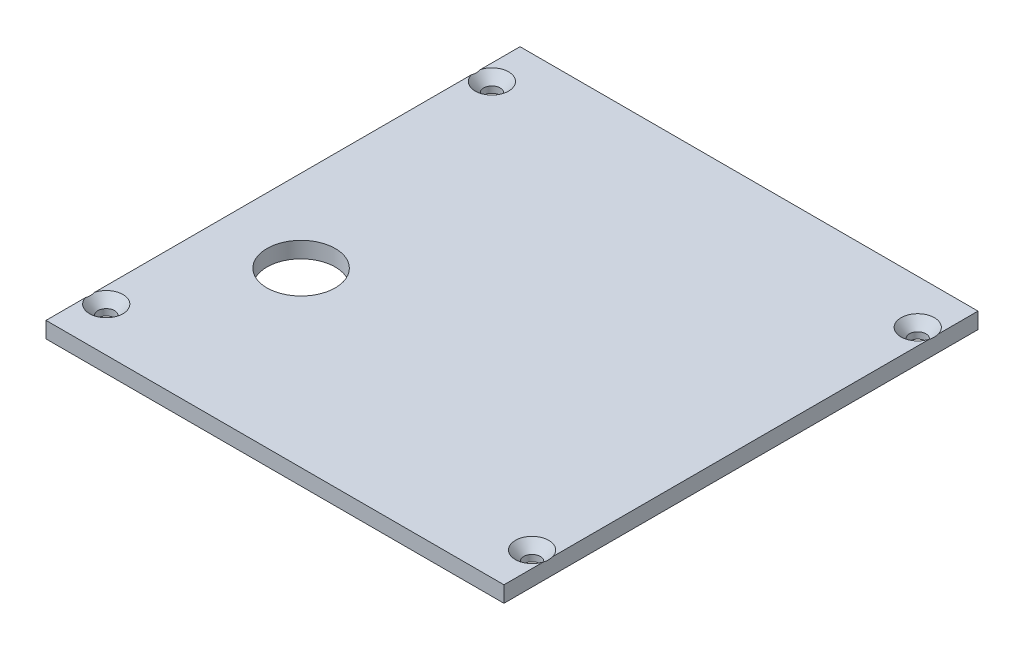
SolidWorks part; units mm, degrees
material "Acrylic (Medium-high impact)"
ref_plane "Front Plane" through (0, 0, 0) normal (0, 0, 1) x (1, 0, 0)
ref_plane "Top Plane" through (0, 0, 0) normal (0, 1, 0) x (1, 0, 0)
ref_plane "Right Plane" through (0, 0, 0) normal (1, 0, 0) x (0, 0, -1)
sketch "Sketch1" plane through (0, 0, 0) normal (0, 1, 0) x (1, 0, 0)
  line L1 (45.2437, 46.8313) -> (-45.2438, 46.8312)
  line L2 (45.2437, 46.8313) -> (45.2437, -46.8312)
  line L3 (45.2437, -46.8312) -> (-45.2438, -46.8313)
  line L4 (-45.2438, 46.8312) -> (-45.2438, -46.8313)
  line L5 (45.2437, 46.8313) -> (-45.2438, -46.8313) construction
  line L6 (45.2437, -46.8312) -> (-45.2438, 46.8312) construction
  point P0 (0, 0)
  dimension "D1" = 90.4875
  dimension "D2" = 93.6625
extrude "Boss-Extrude1" add sketch "Sketch1" along normal blind 3.175
hole_wizard "CSK for #4 Flat Head Machine Screw1" positions "Sketch2" profile "Sketch3" countersink size "#4" standard "ANSI Inch" end condition through all
sketch "Sketch2" plane through (0, 3.175, 0) normal (0, 1, 0) x (1, 0, 0)
  line L1 (-42.0688, 38.1) -> (42.0688, 38.1)
  line L2 (-42.0688, 38.1) -> (-42.0688, -38.1)
  line L3 (-42.0688, -38.1) -> (42.0688, -38.1)
  line L4 (42.0688, 38.1) -> (42.0688, -38.1)
  line L5 (-42.0688, 38.1) -> (42.0688, -38.1) construction
  line L6 (-42.0688, -38.1) -> (42.0688, 38.1) construction
  line L7 (-45.2438, 46.8312) -> (-45.2438, -46.8313) construction
  point P2 (42.0688, -38.1)
  point P9 (-42.0688, 38.1)
  point P10 (-42.0688, -38.1)
  point P11 (42.0688, 38.1)
  point P43 (0, 0)
  point P44 (0, 0)
  point P45 (0, 0)
  point P46 (0, 0)
  dimension "D1" = 3.175
  dimension "D2" = 76.2
sketch "Sketch3" plane through (42.0688, 3.175, 38.1) normal (1, 0, 0) x (0, 0, 1)
  line L0 (0, 0) -> (0, 3.175)
  line L1 (0, 3.175) -> (1.6319, 3.175)
  line L2 (1.6319, 3.175) -> (1.6319, 1.9178)
  line L3 (1.6319, 1.9178) -> (3.2991, 0)
  line L5 (3.2991, 0) -> (0, 0)
  line L6 (-1.632, 1.9178) -> (-3.2991, 0) construction
  line L11 (0, -6.35) -> (0, 107.95) construction
  dimension "Thru Hole Dia." = 3.2639
  dimension "Thru Hole Depth" = 3.175
  dimension "Near C'Sink Dia." = 6.5982
  dimension "Near C'Sink Angle" = 82
sketch "Sketch4" plane through (0, 3.175, 0) normal (0, 1, 0) x (1, 0, 0)
  line L0 (-38.8938, -1000.3703) -> (-38.8938, 48999.6297) construction
  line L1 (-45.2438, 37.2037) -> (-45.2438, -37.2037) construction
  line L2 (-45.2438, 37.2037) -> (-45.2438, -37.2037) construction
  circle A0 centre (-28.9719, -12.7) radius 6.7469
  point P6 (-45.2438, 0)
  dimension "D1" = 13.4937
  dimension "D3" = 3.175
  dimension "D2" = 6.35
  dimension "D4" = 12.7
extrude "Cut-Extrude1" cut sketch "Sketch4" against normal through all
